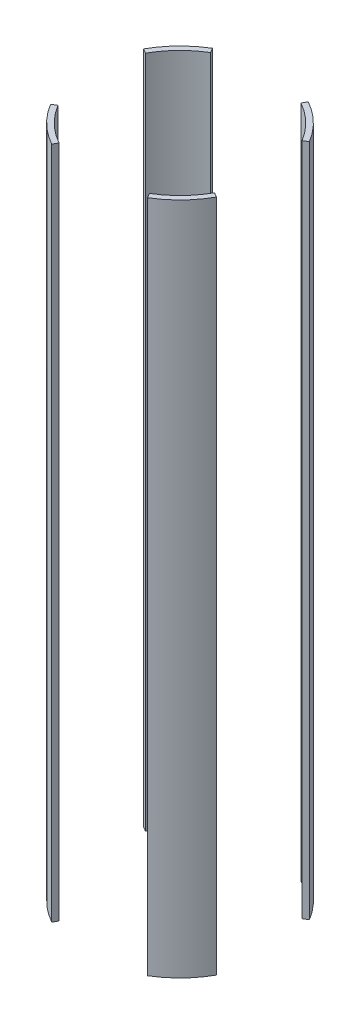
SolidWorks part; units mm, degrees
material "6061-T6 (SS)"
ref_plane "Front Plane" through (0, 0, 0) normal (0, 0, 1) x (1, 0, 0)
ref_plane "Top Plane" through (0, 0, 0) normal (0, 1, 0) x (1, 0, 0)
ref_plane "Right Plane" through (0, 0, 0) normal (1, 0, 0) x (0, 0, -1)
sketch "Sketch2" plane through (0, 0, 0) normal (0, 1, 0) x (1, 0, 0)
  circle A0 centre (0, 0) radius 88.9
  circle A1 centre (0, 0) radius 83.82
  dimension "D1" = 177.8
  dimension "D2" = 167.64
extrude "Boss-Extrude1" add sketch "Sketch2" along normal mid plane 635
sketch "Sketch3" plane through (0, 0, 0) normal (0, 1, 0) x (1, 0, 0)
  line L0 (0, 0) -> (169.6618, 101.6776)
  line L1 (-58.1167, 96.9749) -> (0, 0)
  line L2 (0, 0) -> (53.9, 96.9749)
  line L3 (53.9, 96.9749) -> (-58.1167, 96.9749)
  line L4 (0, 0) -> (70.9917, -118.4586)
  line L5 (70.9917, -118.4586) -> (-65.8409, -118.4586)
  line L6 (-65.8409, -118.4586) -> (0, 0)
  line L7 (169.6618, 101.6776) -> (169.6618, -94.3004)
  line L8 (169.6618, -94.3004) -> (0, 0)
  line L9 (0, 0) -> (-123.7413, 68.7771)
  line L10 (-123.7413, 68.7771) -> (-123.7413, -74.1577)
  line L11 (-123.7413, -74.1577) -> (0, 0)
  dimension "D1" = 60
  dimension "D2" = 60
  dimension "D3" = 60
  dimension "D4" = 60
  dimension "D5" = 30
  dimension "D6" = 30
extrude "Cut-Extrude1" cut sketch "Sketch3" against normal through all both and the other way through all contours L8 L7 L0 | L2 L3 L1 | L10 L11 L9 | L6 L5 L4
sketch "Sketch4" plane through (0, -317.5, 0) normal (0, -1, 0) x (1, 0, 0)
  circle A0 centre (0, 0) radius 88.9
  circle A1 centre (0, 0) radius 76.2
  dimension "D1" = 152.4
  dimension "D2" = 177.8
extrude "Boss-Extrude2" [suppressed] add sketch "Sketch4" against normal blind 12.7
equation "\"D1@Boss-Extrude1\"=3*12"
